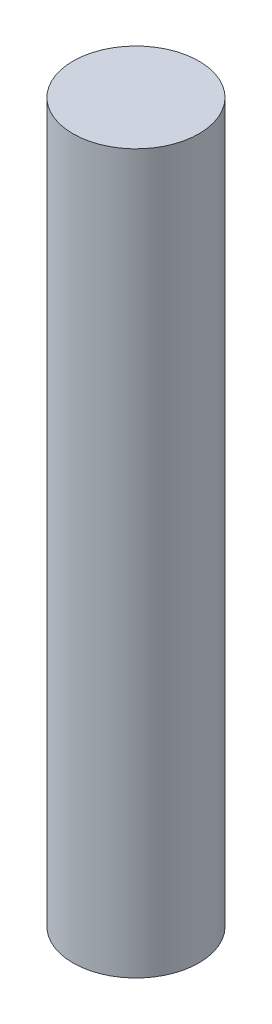
SolidWorks part; units mm, degrees
material "AISI 304"
ref_plane "Ön Düzlem" through (0, 0, 0) normal (0, 0, 1) x (1, 0, 0)
ref_plane "Üst Düzlem" through (0, 0, 0) normal (0, 1, 0) x (1, 0, 0)
ref_plane "Sağ Düzlem" through (0, 0, 0) normal (1, 0, 0) x (0, 0, -1)
sketch "Çizim1" plane through (0, 0, 0) normal (0, 1, 0) x (1, 0, 0)
  circle A0 centre (0, 0) radius 5
  dimension "D1" = 10
extrude "Yükseklik-Ekstrüzyon1" add sketch "Çizim1" along normal blind 57
